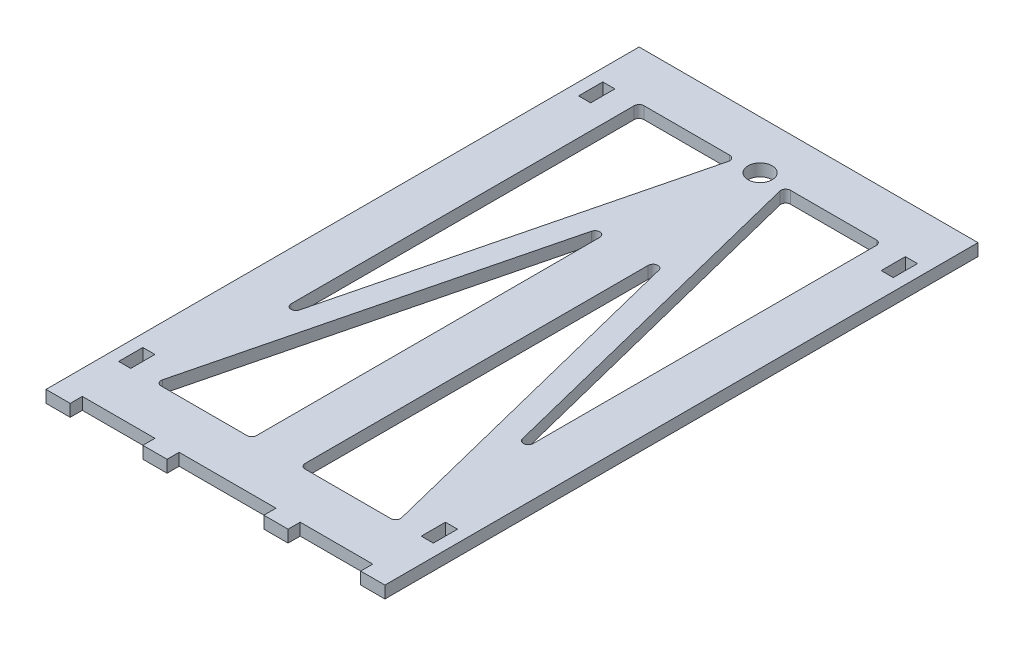
SolidWorks part; units mm, degrees
material "Beech"
ref_plane "Front Plane" through (0, 0, 0) normal (0, 0, 1) x (1, 0, 0)
ref_plane "Top Plane" through (0, 0, 0) normal (0, 1, 0) x (1, 0, 0)
ref_plane "Right Plane" through (0, 0, 0) normal (1, 0, 0) x (0, 0, -1)
sketch "Sketch1" plane through (0, 0, 0) normal (0, 1, 0) x (1, 0, 0)
  line L0 (0, 0) -> (177.8, 0)
  line L1 (0, 0) -> (0, 304.8)
  line L2 (177.8, 0) -> (177.8, 304.8)
  line L3 (0, 304.8) -> (177.8, 304.8)
  line L4 (0, 0) -> (12.7, 0)
  line L5 (0, 0) -> (0, -6.35)
  line L6 (12.7, 0) -> (12.7, -6.35)
  line L7 (0, -6.35) -> (12.7, -6.35)
  line L8 (177.8, 0) -> (165.1, 0)
  line L9 (177.8, 0) -> (177.8, -6.35)
  line L10 (165.1, 0) -> (165.1, -6.35)
  line L11 (177.8, -6.35) -> (165.1, -6.35)
  line L12 (127, 0) -> (114.3, 0)
  line L13 (127, 0) -> (127, -6.35)
  line L14 (114.3, 0) -> (114.3, -6.35)
  line L15 (127, -6.35) -> (114.3, -6.35)
  line L16 (50.8, 0) -> (63.5, 0)
  line L17 (50.8, 0) -> (50.8, -6.35)
  line L18 (63.5, 0) -> (63.5, -6.35)
  line L19 (50.8, -6.35) -> (63.5, -6.35)
  line L20 (165.1, 279.4) -> (171.45, 279.4)
  line L21 (165.1, 279.4) -> (165.1, 266.7)
  line L22 (171.45, 279.4) -> (171.45, 266.7)
  line L23 (165.1, 266.7) -> (171.45, 266.7)
  line L24 (6.35, 279.4) -> (12.7, 279.4)
  line L25 (6.35, 279.4) -> (6.35, 266.7)
  line L26 (12.7, 279.4) -> (12.7, 266.7)
  line L27 (6.35, 266.7) -> (12.7, 266.7)
  line L28 (6.35, 38.1) -> (12.7, 38.1)
  line L29 (6.35, 38.1) -> (6.35, 25.4)
  line L30 (12.7, 38.1) -> (12.7, 25.4)
  line L31 (6.35, 25.4) -> (12.7, 25.4)
  line L32 (165.1, 38.1) -> (171.45, 38.1)
  line L33 (165.1, 38.1) -> (165.1, 25.4)
  line L34 (171.45, 38.1) -> (171.45, 25.4)
  line L35 (165.1, 25.4) -> (171.45, 25.4)
  line L36 (101.6, 279.4) -> (152.4, 279.4)
  line L37 (152.4, 279.4) -> (152.4, 76.2)
  line L38 (152.4, 76.2) -> (101.6, 279.4)
  line L39 (101.6, 228.6) -> (101.6, 25.4)
  line L40 (101.6, 25.4) -> (152.4, 25.4)
  line L41 (152.4, 25.4) -> (101.6, 228.6)
  line L42 (76.2, 279.4) -> (25.4, 279.4)
  line L43 (25.4, 279.4) -> (25.4, 76.2)
  line L44 (25.4, 76.2) -> (76.2, 279.4)
  line L45 (76.2, 228.6) -> (76.2, 25.4)
  line L46 (76.2, 25.4) -> (25.4, 25.4)
  line L47 (25.4, 25.4) -> (76.2, 228.6)
  circle A0 centre (88.9, 279.4) radius 6.35
  point P21 (88.9, 304.8)
  dimension "D8" = 12.7
  dimension "D1" = 177.8
  dimension "D2" = 6.35
  dimension "D3" = 12.7
  dimension "D4" = 50.8
  dimension "D5" = 50.8
  dimension "D6" = 304.8
  dimension "D7" = 25.4
  dimension "D9" = 25.4
  dimension "D10" = 25.4
  dimension "D11" = 12.7
  dimension "D12" = 12.7
  dimension "D13" = 203.2
  dimension "D14" = 50.8
  dimension "D15" = 50.8
extrude "Front Panel" add sketch "Sketch1" along normal blind 6.35
fillet "Fillet1" radius 2.54 12 edges at (25.4, 3.175, -76.2) (152.4, 3.175, -76.2) (25.4, 3.175, -25.4) (76.2, 3.175, -25.4) (101.6, 3.175, -25.4) (152.4, 3.175, -25.4) (76.2, 3.175, -228.6) (101.6, 3.175, -228.6) (25.4, 3.175, -279.4) (76.2, 3.175, -279.4) (101.6, 3.175, -279.4) (152.4, 3.175, -279.4)
equation "\"CageLeftBottomEdge\"=22.11mm"
equation "\"CageLeftTopEdge\"=22.11mm"
equation "\"CageRightBottomEdge\"=21.63mm"
equation "\"CageRightTopEdge\"=21.63mm"
equation "\"CageHeight\"=86.04mm"
equation "\"CageLength\"=73.76mm"
equation "\"CageTopScrewClearance\"=10mm"
equation "\"CageBottomScrewClearance\"=25mm"
equation "\"CageLeftTopDepth\"= 11.65mm"
equation "\"CageLeftBottomDepth\"=11.11mm"
equation "\"CageLeftTopHeight\"=8.56175mm"
equation "\"CageLeftBottomHeight\"=16mm"
equation "\"CageRightTopDepth\"= 11.05mm"
equation "\"CageRightBottomDepth\"=10.58mm"
equation "\"CageRightTopHeight\"=9.6mm"
equation "\"CageRightBottomHeight\"=15.49mm"
equation "\"CageLeftTopChannelDepth\"=2.41908mm"
equation "\"CageLeftBottomChannelDepth\"=2.588mm"
equation "\"CageLeftChannelHeight\"=11.7mm"
equation "\"CageRightTopChannelDepth\"=2.32mm"
equation "\"CageRightBottomChannelDepth\"=2.318mm"
equation "\"CageRightChannelHeight\"=10mm"
equation "\"CageChanRelHeight\"=23.99mm"
equation "\"CageChanRelDepth\"=5.492mm"
equation "\"CageChamberRadius\"=16.261mm"
equation "\"CageScrewDiameter\"=4.8mm"
equation "\"CageSetScrewDiameter\"=3.5mm"
equation "\"CageAxleRadius\"=6.639mm"
equation "\"CageAxleKeyHeight\"=1.619mm"
equation "\"CageAxleKeyWidth\"=2.662mm"
equation "\"CageHoseWindowWidth\"=16.29mm"
equation "\"CageHoseWindowHeight\"=26.5mm"
equation "\"CageHoseWindow-Edge\"=8.89mm"
equation "\"CageScrew-VerticalEdge\"=5.0mm"
equation "\"CageScrew-HorizontalEdge\"=7.5mm"
equation "\"CageScrew-HoseCornerScrewEdge\"=4.45mm"
equation "\"CageAxle-BottomEdge\"=56.05mm"
equation "\"CageAxle-FrontEdge\"=46.03mm"
equation "\"CageBackSetScrew-Axle\"=40mm"
equation "\"CageFrontSetScrew-Axle\"=22mm"
equation "\"CageVelocityWindow-BackEdge\"=34.8mm"
equation "\"CageVelocityWindow-BottomEdge\"=27.55mm"
equation "\"CageVelocityWindowHeight\"=22.29mm"
equation "\"CageVelocityWindowWidth\"=12.61mm"
equation "\"TriggerSlot-BottomEdge\"=6.35mm"
equation "\"TriggerSlot-FrontEdge\"=15mm"
equation "\"TriggerSlotSize\"=6.7mm"
equation "\"TriggerRackOffset\"=6mm"
equation "\"TriggerSlotSizeInt\"=.25in"
equation "\"MotorMountLegLength\"=.25in"
equation "\"GearOffset\"=.264907in"
equation "\"TriggerSlotSpacing\"=.25in"
equation "\"TriggerMiniSlotWidth\"=3.5mm"
equation "\"TriggerRackWidth\"=6.5mm"
equation "\"pandiscradius\"=14in"
equation "\"towermaterialwidth\"=.25in"
equation "\"towerslotlength\"=.5in"
equation "\"towermarkerspace\"=5in"
equation "\"towerslothorizoffset\"=1in"
equation "\"towerslothorizspacing\"=2in"
equation "\"towerslotvertoffset\"=3in"
equation "\"towerslotvertspacing\"=1in"
equation "\"towerheight\"=12in"
equation "\"towerupslot\"=1in"
equation "\"D1@Sketch1\"=(\"towerslothorizoffset\"+\"towerslothorizspacing\"+\"towerslotlength\")*2"
equation "\"D2@Sketch1\"=\"towermaterialwidth\""
equation "\"D3@Sketch1\"=\"towerslotlength\""
equation "\"D4@Sketch1\"=\"towerslothorizspacing\""
equation "\"D5@Sketch1\"=\"towerslothorizspacing\""
equation "\"D6@Sketch1\"=\"towerheight\""
equation "\"D7@Sketch1\"=\"towerupslot\""
equation "\"toweraxle\"=.5in"
equation "\"D8@Sketch1\"=\"toweraxle\""
equation "\"D9@Sketch1\"=\"towerupslot\""
equation "\"D10@Sketch1\"= \"towerupslot\""
equation "\"D1@Front Panel\"=\"towermaterialwidth\""
equation "\"stepperouterrad\"=10mm"
equation "\"stepperscrewsize\"=3.45mm"
equation "\"stepperscrewc2c\"=49.5mm"
equation "\"stepperdepthoffset\"=24mm"
equation "\"stepperhorizoffset\"=22.91mm"
equation "\"shaftslotOD\"=18.8mm"
equation "\"shaftslotID\"=13.28mm"
equation "\"shaftkeywidth\"=2.67mm"
equation "\"shaftkeydepth\"=1.8mm"
equation "\"shaftcollartotaldepth\"=9.71mm"
equation "\"shaftsquaredepth\"=6mm"
equation "\"shaftsetscrewsize\"=3.5mm"
equation "\"shaftkeytightdepth\"=1.85mm"
equation "\"shaftslottightID\"=12.78mm"
equation "\"shaftsetscrewoffset\"=9mm"
equation "\"cagecollartotaldepth\"=20mm"
equation "\"cagecollartotalwidth\"=35mm"
equation "\"cagecollarbasedepth\"=4mm"
equation "\"D11@Sketch1\"=\"toweraxle\""
equation "\"D12@Sketch1\"=\"toweraxle\""
equation "\"towerspeedwidth\"=2in"
equation "\"D15@Sketch1\"=\"towerspeedwidth\""
equation "\"towerspeedheight\"=8in"
equation "\"D13@Sketch1\"=\"towerspeedheight\""
equation "\"towerspeedgap\"=2in"
equation "\"D14@Sketch1\"=\"towerspeedgap\""
equation "\"gearhubintdiam\"=30mm"
equation "\"gearhubintwid\"=12.21mm"
equation "\"stepperaxleflat\"=.037in"
equation "\"stepperaxlerad\"=0.11811024in"
equation "\"ajaxaxlesize\"=3.87mm"
equation "\"ajaxinnercut\"=2.3mm"
equation "\"ajaxwidth\"=6.1mm"
equation "\"ajaxdiametral\"=25.8854"
equation "\"ajaxcutoutdepth\"=2.3mm"
equation "\"ajax4020gap\"=29.5mm"
equation "\"ajax4010gap\"=24.5mm"
equation "\"ajax20hubbuffer\"=6.1mm"
equation "\"ajax20hubholeoffset\"=.19685in"
equation "\"ajax20hubholesize\"=.059055in"
equation "\"ajax20cutoutint\"=13.4mm"
equation "\"ajax40hubholesize\"=7.21mm"
equation "\"ajax40hubholeoffset\"=10mm"
equation "\"ajax40hubbuffer\"=8.9mm"
equation "\"ajax40cutoutint\"=32.6mm"
equation "\"bearingpandiscrad\"=6.8in"
equation "\"bearingpandiscang\"=48.75deg"
equation "\"bearingclearholedist\"=4.7345in"
equation "\"bearingclearholesize\"=.5in"
equation "\"bearingclearholeang\"=22.5deg"
equation "\"bearingmountholedist\"=4.25in"
equation "\"bearingwirehole\"=1.5in"
equation "\"no6diam\"=.146in"
equation "\"shortconangle\"=20deg"
equation "\"shortconlen\"=.875in"
equation "\"longconlen\"=1.25in"
equation "\"longconangle\"=15deg"
